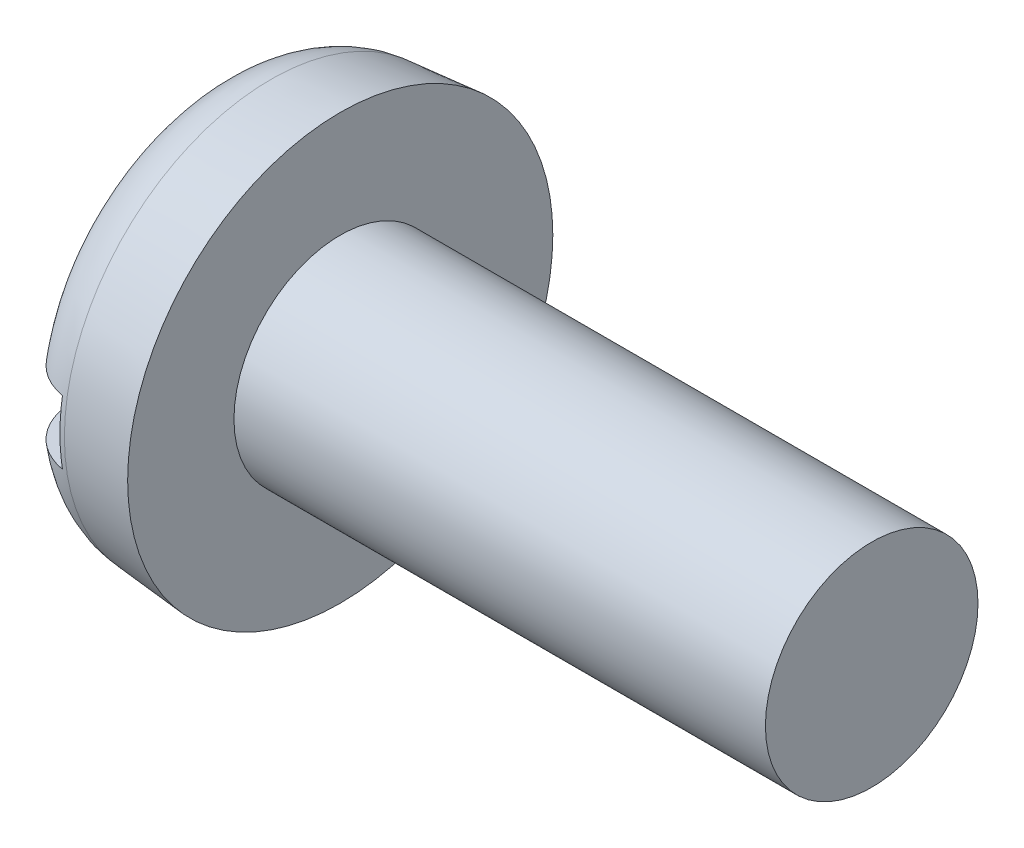
SolidWorks part; units mm, degrees
ref_plane "Plane1" through (0, 0, 0) normal (0, 0, 1) x (1, 0, 0)
ref_plane "Plane2" through (0, 0, 0) normal (0, 1, 0) x (1, 0, 0)
ref_plane "Plane3" through (0, 0, 0) normal (1, 0, 0) x (0, 0, -1)
sketch "BodySke" plane through (0, 0, 0) normal (0, 0, 1) x (1, 0, 0)
  line L0 (2.4, 2) -> (2.4, 4)
  line L1 (0, 0) -> (0, 3.79)
  line L2 (-25.4, 0) -> (127, 0) construction
  line L3 (12.4, 0) -> (0, 0)
  line L4 (2.4, 2) -> (12.4, 2)
  line L5 (12.4, 2) -> (12.4, 0)
  line L6 (0, 3.79) -> (2.4, 4)
  line L9 (3.1, 3.5875) -> (3.1, -5.9375) construction
  line L10 (2.4, 6.35) -> (2.4, -3.175) construction
  dimension "Head_ht" = 2.4
  dimension "Diameter" = 4
  dimension "Length" = 10
  dimension "Head_dia" = 8
  dimension "Advance" = 0.7
  dimension "Thread_nom" = 10
  dimension "Head_side_angle" = 5
revolve "Base-Revolve" add sketch "BodySke"
cosmetic thread "ThreadCosmetic"
fillet "Fillet1" [suppressed] radius 0.2
fillet "Fillet2" radius 1.2 1 edges at (0, 0, 3.79)
sketch "Sketch2" plane through (0, 0, 0) normal (1, 0, 0) x (0, 0, -1)
  line L0 (4, -0.6) -> (-4, -0.6)
  line L1 (4, -0.6) -> (4, 0.6)
  line L2 (-4, 0.6) -> (4, 0.6)
  line L3 (-4, 0.6) -> (-4, -0.6)
  dimension "D1" = 8
  dimension "D2" = 4
  dimension "Slot_width" = 1.2
  dimension "D3" = 0.6
extrude "Slot" cut sketch "Sketch2" along normal blind 1
sketch "ThdSchSke" plane through (0, 0, 0) normal (0, 0, 1) x (1, 0, 0)
  line L0 (3.8, -1.61) -> (3.5269, -2)
  line L1 (3.8, -1.61) -> (4.0731, -2)
  line L2 (4.0731, -2) -> (4.0731, -2.5)
  line L3 (-3.175, 0) -> (5.1513, 0) construction
  line L5 (4.0731, -2.5) -> (3.5269, -2.5)
  line L6 (3.5269, -2.5) -> (3.5269, -2)
  dimension "Thread_minor" = 3.22
  dimension "Diameter" = 4
  dimension "Start" = 3.8
  dimension "SideAngle" = 55
  dimension "VeeAngle" = 70
  dimension "Overcut" = 5
revolve "ThreadSchematic" [suppressed] cut sketch "ThdSchSke" angle 360 about L3
pattern_linear "ThdSchPat" [suppressed]
equation "\"D1@Sketch2\" = \"Head_dia@BodySke\""
equation "\"D2@Sketch2\" = \"D1@Sketch2\" / 2"
equation "\"D3@Sketch2\" = \"Slot_width@Sketch2\" / 2"
equation "\"Thread_length@ThreadCosmetic\" = ((sgn( (\"Length@BodySke\" - \"Advance@BodySke\" * 2.0 ) - \"Thread_nom@BodySke\" )-1)*( (\"Length@BodySke\" - \"Advance@BodySke\"  * 2.0) - \"Thread_nom@BodySke\" ))/-2+ \"Thread_nom@BodySke\""
equation "\"Thread_minor@ThdSchSke\" = \"Thread_minor@ThreadCosmetic\""
equation "\"Diameter@ThdSchSke\" = \"Diameter@BodySke\""
equation "\"Overcut@ThdSchSke\" = \"Diameter@BodySke\" * 1.25"
equation "\"Start@ThdSchSke\" = \"Head_ht@BodySke\" + \"Length@BodySke\" - \"Thread_length@ThreadCosmetic\"  '---Non-countersunk---"
equation "\"Num_threads@ThdSchPat\" = int( \"Thread_length@ThreadCosmetic\" / \"Advance@BodySke\" + 0.999 )  + 1"
equation "\"Advance@ThdSchPat\" = \"Thread_length@ThreadCosmetic\" /  (\"Num_threads@ThdSchPat\" - 1) 'relax it"
